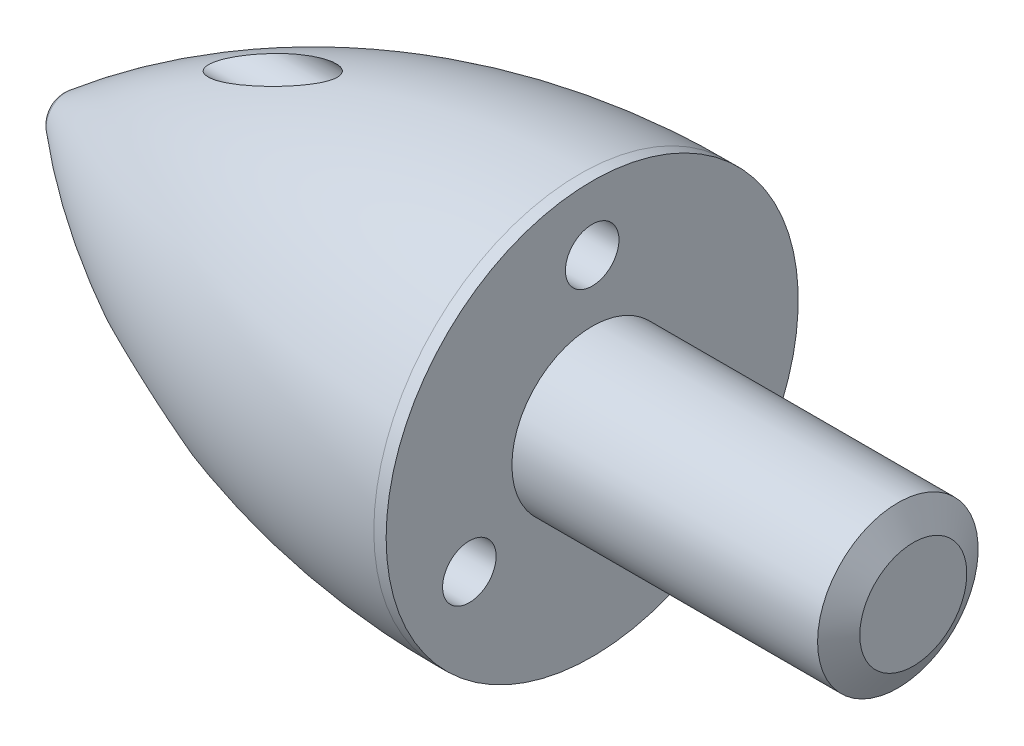
SolidWorks part; units mm, degrees
material "1.4404 (X2CrNiMo17-12-2)"
ref_plane "Front Plane" through (0, 0, 0) normal (0, 0, 1) x (1, 0, 0)
ref_plane "Top Plane" through (0, 0, 0) normal (0, 1, 0) x (1, 0, 0)
ref_plane "Right Plane" through (0, 0, 0) normal (1, 0, 0) x (0, 0, -1)
ref_axis "Axis1" through (-88.99, 0, 0) along (1, 0, 0)
sketch "Sketch1" plane through (0, 0, 0) normal (0, 0, 1) x (1, 0, 0)
  line L0 (0, 3.85) -> (0, 1.5)
  line L1 (0, 1.5) -> (5.7113, 1.5)
  line L2 (5.7113, 1.5) -> (6, 1)
  line L3 (6, 1) -> (6, 0)
  line L4 (-88.99, 0) -> (88.99, 0) construction
  line L5 (-10, 0) -> (6, 0)
  line L6 (0, 3.85) -> (-0.2303, 3.85)
  arc A0 (-10, 0) -> (-9.8196, 0.3845) centre (-9.5, 0) cw
  arc A1 (-9.8196, 0.3845) -> (-0.2303, 3.85) centre (-0.2303, -11.15) cw
  point P13 (0, 0)
  dimension "D5" = 0.5
  dimension "D8" = 15
  dimension "D1" = 1.5
  dimension "D2" = 30
  dimension "D3" = 6
  dimension "D4" = 3.85
  dimension "D6" = 10
  dimension "D7" = 0.5
revolve "Revolve1" add sketch "Sketch1" angle 360 about axis through (-88.99, 0, 0) along (1, 0, 0)
hole_wizard "Ø1.0mm Dowel Hole1" positions "Sketch4" profile "Sketch5" hole size "Ø1.0" standard "DIN"
sketch "Sketch4" plane through (0, 0, 0) normal (1, 0, 0) x (0, 0, -1)
  line L0 (0, 2.65) -> (0, 0)
  circle A0 centre (0, 0) radius 2.65
  point P0 (0, 2.65)
  dimension "D1" = 5.3
sketch "Sketch5" plane through (0, 2.65, 0) normal (0, 1, 0) x (0, 0, -1)
  line L0 (0, 0) -> (0, 8.8004)
  line L1 (0, 8.8004) -> (0.5, 8.5)
  line L2 (0.5, 8.5) -> (0.5, 0)
  line L5 (0.5, 0) -> (0, 0)
  line L10 (0, 8.8004) -> (-0.5, 8.5) construction
  line L11 (0, -6.35) -> (0, 107.95) construction
  dimension "Hole Dia." = 1
  dimension "Hole Depth" = 8.5
  dimension "Drill Angle" = 118
pattern_circular "CirPattern1" count 3 over 360 about axis through (0, 0, 0) along (1, 0, 0) of "Ø1.0mm Dowel Hole1"
